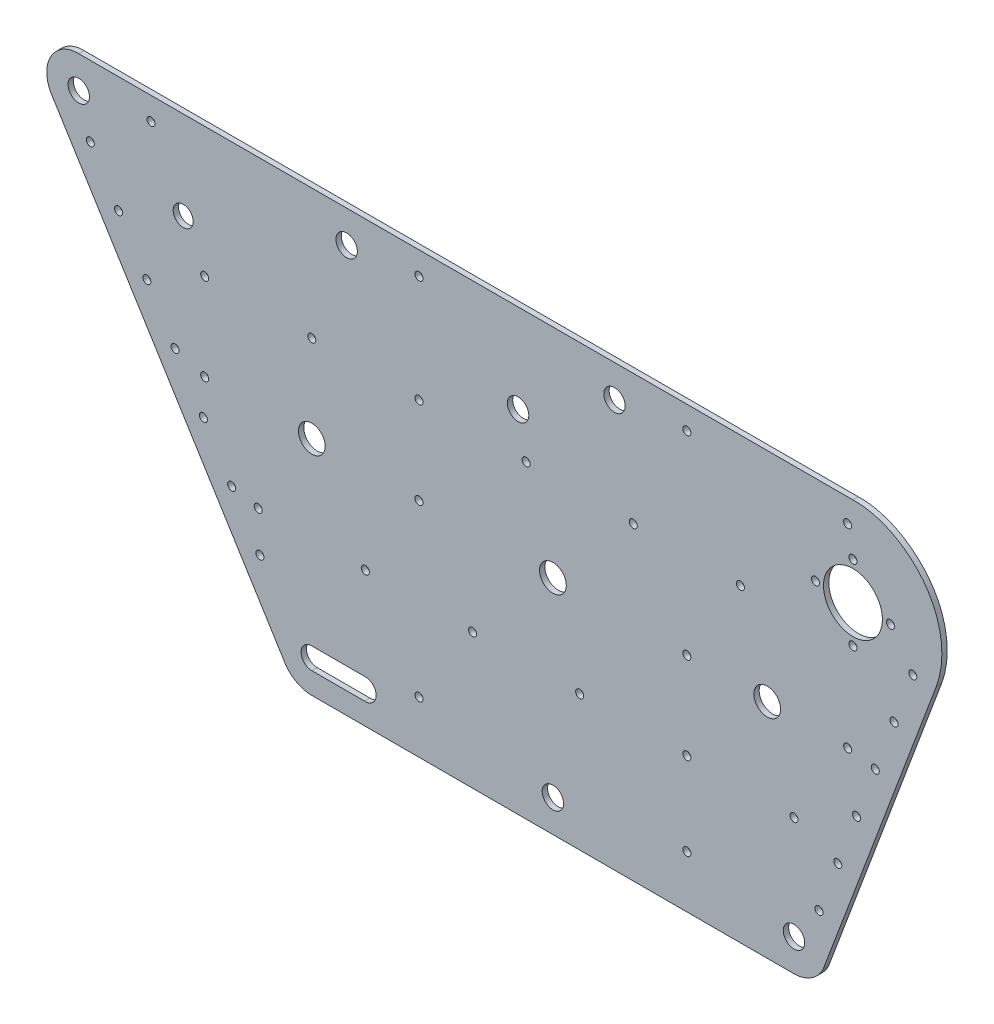
SolidWorks part; units mm, degrees
ref_plane "Front Plane" through (0, 0, 0) normal (0, 0, 1) x (1, 0, 0)
ref_plane "Top Plane" through (0, 0, 0) normal (0, 1, 0) x (1, 0, 0)
ref_plane "Right Plane" through (0, 0, 0) normal (1, 0, 0) x (0, 0, -1)
sketch "Sketch2" plane through (0, 0, 0) normal (0, 0, 1) x (1, 0, 0)
  line L0 (-106.0052, 144.9436) -> (182.9631, 145.1977)
  line L1 (160.992, -19) -> (-18.999, -19)
  line L2 (171.9001, -12) -> (214.069, 100.3323)
  line L3 (-18.999, -3) -> (1, -3)
  line L4 (0.9999, -11) -> (-18.9991, -11)
  line L5 (-29.7001, -12.4286) -> (-116.0855, 126.6112)
  line L6 (-18.9991, -18) -> (-18.8768, -17.9993)
  ellipse E0 centre (-105.9947, 133) end of major axis (-105.9947, 137) minor radius 3.9998
  ellipse E1 centre (160.992, -7) end of major axis (160.992, -3) minor radius 3.9998
  ellipse E2 centre (-18.9991, -7) end of major axis (-18.9991, -11) minor radius 3.9998 (-18.999, -3) -> (-18.9991, -11) ccw
  ellipse E3 centre (182.9908, 112) end of major axis (182.9908, 123) minor radius 10.9995
  ellipse E4 centre (-105.9947, 133) end of major axis (-105.9947, 144.9436) minor radius 11.943 (-106.0052, 144.9436) -> (-116.0855, 126.6112) ccw
  ellipse E5 centre (182.9908, 112) end of major axis (182.9909, 145.1977) minor radius 33.196 (214.069, 100.3323) -> (182.9617, 145.1977) ccw
  ellipse E6 centre (1, -7) end of major axis (1, -3) minor radius 3.9998 (0.9999, -11) -> (1, -3) ccw
  ellipse E7 centre (182.9908, 126) end of major axis (182.9908, 127.5) minor radius 1.4999
  ellipse E8 centre (196.9901, 112) end of major axis (196.9901, 113.5) minor radius 1.4999
  ellipse E9 centre (168.9915, 112) end of major axis (168.9915, 113.5) minor radius 1.4999
  ellipse E10 centre (182.9908, 98) end of major axis (182.9908, 99.5) minor radius 1.4999
  ellipse E11 centre (-18.9991, -7) end of major axis (-18.999, 5) minor radius 11.9994 (-29.7019, -12.4256) -> (-18.999, -19) ccw
  ellipse E12 centre (160.992, -7) end of major axis (160.992, 5) minor radius 11.9994 (160.992, -19) -> (171.9001, -12) ccw
  ellipse E13 centre (120.9939, 0.5) end of major axis (120.994, 2) minor radius 1.4999
  ellipse E14 centre (20.9989, 0.5) end of major axis (20.9989, 2) minor radius 1.4999
  ellipse E15 centre (120.9939, 64) end of major axis (120.994, 65.5) minor radius 1.4999
  ellipse E16 centre (20.9989, 64) end of major axis (20.9989, 65.5) minor radius 1.4999
  ellipse E17 centre (-58.997, 64) end of major axis (-58.997, 65.5) minor radius 1.4999
  ellipse E18 centre (180.9909, 64) end of major axis (180.9909, 65.5) minor radius 1.4999
  ellipse E19 centre (-78.996, 136.5) end of major axis (-78.996, 138) minor radius 1.4999
  ellipse E20 centre (20.9989, 136.5) end of major axis (20.9989, 138) minor radius 1.4999
  ellipse E21 centre (120.9939, 136.5) end of major axis (120.994, 138) minor radius 1.4999
  ellipse E22 centre (60.9969, 96.5) end of major axis (60.9969, 98) minor radius 1.4999
  ellipse E23 centre (140.9929, 96.5) end of major axis (140.9929, 98) minor radius 1.4999
  ellipse E24 centre (160.992, 31.5) end of major axis (160.992, 33) minor radius 1.4999
  ellipse E25 centre (80.996, 31.5) end of major axis (80.996, 33) minor radius 1.4999
  ellipse E26 centre (-18.9991, 96.5) end of major axis (-18.9991, 98) minor radius 1.4999
  ellipse E27 centre (-38.998, 31.5) end of major axis (-38.998, 33) minor radius 1.4999
  ellipse E28 centre (-18.9991, 64) end of major axis (-18.999, 69) minor radius 4.9997
  ellipse E29 centre (70.9964, 64) end of major axis (70.9965, 69) minor radius 4.9997
  ellipse E30 centre (150.9924, 64) end of major axis (150.9924, 69) minor radius 4.9997
  ellipse E31 centre (-101.6892, 118.5984) end of major axis (-101.6892, 120.0984) minor radius 1.4999
  ellipse E32 centre (-91.1347, 101.6106) end of major axis (-91.1347, 103.1106) minor radius 1.4999
  ellipse E33 centre (-80.5803, 84.623) end of major axis (-80.5803, 86.123) minor radius 1.4999
  ellipse E34 centre (-70.0255, 67.6347) end of major axis (-70.0255, 69.1347) minor radius 1.4999
  ellipse E35 centre (-59.4708, 50.6466) end of major axis (-59.4708, 52.1466) minor radius 1.4999
  ellipse E36 centre (-48.9163, 33.6588) end of major axis (-48.9163, 35.1588) minor radius 1.4999
  ellipse E37 centre (-38.3619, 16.6713) end of major axis (-38.3619, 18.1713) minor radius 1.4999
  ellipse E38 centre (205.3225, 99.7958) end of major axis (205.3225, 101.2958) minor radius 1.4999
  ellipse E39 centre (198.3244, 81.0602) end of major axis (198.3244, 82.5602) minor radius 1.4999
  ellipse E40 centre (191.3265, 62.3248) end of major axis (191.3265, 63.8248) minor radius 1.4999
  ellipse E41 centre (184.3286, 43.5896) end of major axis (184.3286, 45.0896) minor radius 1.4999
  ellipse E42 centre (177.3307, 24.8545) end of major axis (177.3307, 26.3545) minor radius 1.4999
  ellipse E43 centre (170.3325, 6.1186) end of major axis (170.3325, 7.6186) minor radius 1.4999
  ellipse E44 centre (180.9909, 136.5) end of major axis (180.9909, 138) minor radius 1.4999
  ellipse E45 centre (20.9989, 96.5) end of major axis (20.9989, 98) minor radius 1.4999
  ellipse E46 centre (100.995, 96.5) end of major axis (100.995, 98) minor radius 1.4999
  ellipse E47 centre (-58.9971, 96.5) end of major axis (-58.997, 98) minor radius 1.4999
  ellipse E48 centre (0.9999, 31.5) end of major axis (1, 33) minor radius 1.4999
  ellipse E49 centre (40.9979, 31.5) end of major axis (40.9979, 33) minor radius 1.4999
  ellipse E50 centre (120.9939, 31.5) end of major axis (120.994, 33) minor radius 1.4999
  ellipse E51 centre (-66.9967, 112) end of major axis (-66.9966, 115.75) minor radius 3.7498
  ellipse E52 centre (57.9971, 112) end of major axis (57.9971, 116) minor radius 3.9998
  ellipse E53 centre (-5.9997, 133) end of major axis (-5.9997, 137) minor radius 3.9998
  ellipse E54 centre (93.9952, 133) end of major axis (93.9952, 137) minor radius 3.9998
  ellipse E55 centre (70.9964, -7) end of major axis (70.9965, -3) minor radius 3.9998
sketch "Sketch3" plane through (0, 0, 0) normal (0, 0, 1) x (1, 0, 0)
  line L0 (-106.0052, 144.9436) -> (182.9631, 145.1977)
  line L1 (214.069, 100.3323) -> (171.9001, -12)
  line L2 (160.992, -19) -> (-18.999, -19)
  line L3 (-29.7019, -12.4256) -> (-116.0855, 126.6112)
  ellipse E0 centre (182.9908, 112) end of major axis (182.9909, 145.1977) minor radius 33.196 (214.069, 100.3323) -> (182.9617, 145.1977) ccw construction
  ellipse E1 centre (160.992, -7) end of major axis (160.992, 5) minor radius 11.9994 (160.992, -19) -> (171.9001, -12) ccw construction
  ellipse E2 centre (-18.9991, -7) end of major axis (-18.999, 5) minor radius 11.9994 (-29.7019, -12.4256) -> (-18.999, -19) ccw construction
  ellipse E3 centre (-105.9947, 133) end of major axis (-105.9947, 144.9436) minor radius 11.943 (-106.0052, 144.9436) -> (-116.0855, 126.6112) ccw construction
  spline S0 degree 3 poles (214.069, 100.3323) (217.2028, 108.5816) (216.3843, 131.5138) (195.3828, 145.6087) (182.9631, 145.1977) knots 0 0 0 0 0.416239 1 1 1 1
  spline S1 degree 3 poles (160.992, -19) (165.4579, -19.0688) (170.107, -16.0905) (171.9001, -12) knots 0 0 0 0 1 1 1 1
  spline S2 degree 3 poles (-18.999, -19) (-23.4193, -19.0696) (-27.756, -16.3629) (-29.7019, -12.4256) knots 0 0 0 0 1 1 1 1
  spline S3 degree 3 poles (-106.0052, 144.9436) (-112.924, 145.0927) (-119.6619, 137.0318) (-117.3485, 128.5923) (-116.0855, 126.6112) knots 0 0 0 0 0.715346 1 1 1 1
extrude "Boss-Extrude1" add sketch "Sketch3" along normal blind 2
sketch "Sketch4" plane through (0, 0, 2) normal (0, 0, 1) x (1, 0, 0)
  line L0 (-18.999, -3) -> (1, -3)
  line L1 (20.9989, 0.5) -> (132.767, 0.5) construction
  line L2 (-18.9991, -11) -> (0.7498, -11)
  line L3 (0.9999, -11) -> (-18.9991, -11) construction
  line L4 (132.767, 0.5) -> (4.6834, 0.5) construction
  line L5 (4.6834, 8) -> (132.767, 8) construction
  circle A0 centre (-105.9947, 133) radius 3.9998
  circle A1 centre (-78.996, 136.5) radius 1.4999
  circle A2 centre (-101.6892, 118.5984) radius 1.4999
  circle A3 centre (-91.1347, 101.6106) radius 1.4999
  circle A4 centre (-66.9967, 112) radius 3.7498
  circle A5 centre (-80.5803, 84.623) radius 1.4999
  circle A6 centre (-5.9997, 133) radius 3.9998
  circle A7 centre (20.9989, 136.5) radius 1.4999
  circle A8 centre (20.9989, 96.5) radius 1.4999
  circle A9 centre (-18.9991, 96.5) radius 1.4999
  circle A10 centre (-58.9971, 96.5) radius 1.4999
  circle A11 centre (57.9971, 112) radius 3.9998
  circle A12 centre (60.9969, 96.5) radius 1.4999
  circle A13 centre (182.9908, 112) radius 10.9995
  circle A14 centre (182.9908, 126) radius 1.4999
  circle A15 centre (180.9909, 136.5) radius 1.4999
  circle A16 centre (120.9939, 136.5) radius 1.4999
  circle A17 centre (93.9952, 133) radius 3.9998
  circle A18 centre (100.995, 96.5) radius 1.4999
  circle A19 centre (140.9929, 96.5) radius 1.4999
  circle A20 centre (168.9915, 112) radius 1.4999
  circle A21 centre (196.9901, 112) radius 1.4999
  circle A22 centre (182.9908, 98) radius 1.4999
  circle A23 centre (205.3225, 99.7958) radius 1.4999
  circle A24 centre (198.3244, 81.0602) radius 1.4999
  circle A25 centre (150.9924, 64) radius 4.9997
  circle A26 centre (180.9909, 64) radius 1.4999
  circle A27 centre (191.3265, 62.3248) radius 1.4999
  circle A28 centre (120.9939, 64) radius 1.4999
  circle A29 centre (184.3286, 43.5896) radius 1.4999
  circle A30 centre (70.9964, 64) radius 4.9997
  circle A31 centre (20.9989, 64) radius 1.4999
  circle A32 centre (0.9999, 31.5) radius 1.4999
  circle A33 centre (40.9979, 31.5) radius 1.4999
  circle A34 centre (80.996, 31.5) radius 1.4999
  circle A35 centre (120.9939, 31.5) radius 1.4999
  circle A36 centre (160.992, 31.5) radius 1.4999
  circle A37 centre (177.3307, 24.8545) radius 1.4999
  circle A38 centre (-18.9991, 64) radius 4.9997
  circle A39 centre (-70.0255, 67.6347) radius 1.4999
  circle A40 centre (-58.997, 64) radius 1.4999
  circle A41 centre (-59.4708, 50.6466) radius 1.4999
  circle A42 centre (-48.9163, 33.6588) radius 1.4999
  circle A43 centre (-38.998, 31.5) radius 1.4999
  circle A44 centre (-38.3619, 16.6713) radius 1.4999
  circle A45 centre (20.9989, 0.5) radius 1.4999
  circle A46 centre (70.9964, -7) radius 3.9998
  circle A47 centre (160.992, -7) radius 3.9998
  circle A48 centre (170.3325, 6.1186) radius 1.4999
  circle A49 centre (120.9939, 0.5) radius 1.4999
  arc A50 (-18.999, -3) -> (-18.9991, -11) centre (-18.9988, -7) ccw
  arc A51 (1, -3) -> (0.7498, -11) centre (0.996, -7.0038) cw
  dimension "D1" = 7.5
extrude "Cut-Extrude1" cut sketch "Sketch4" against normal blind 2
